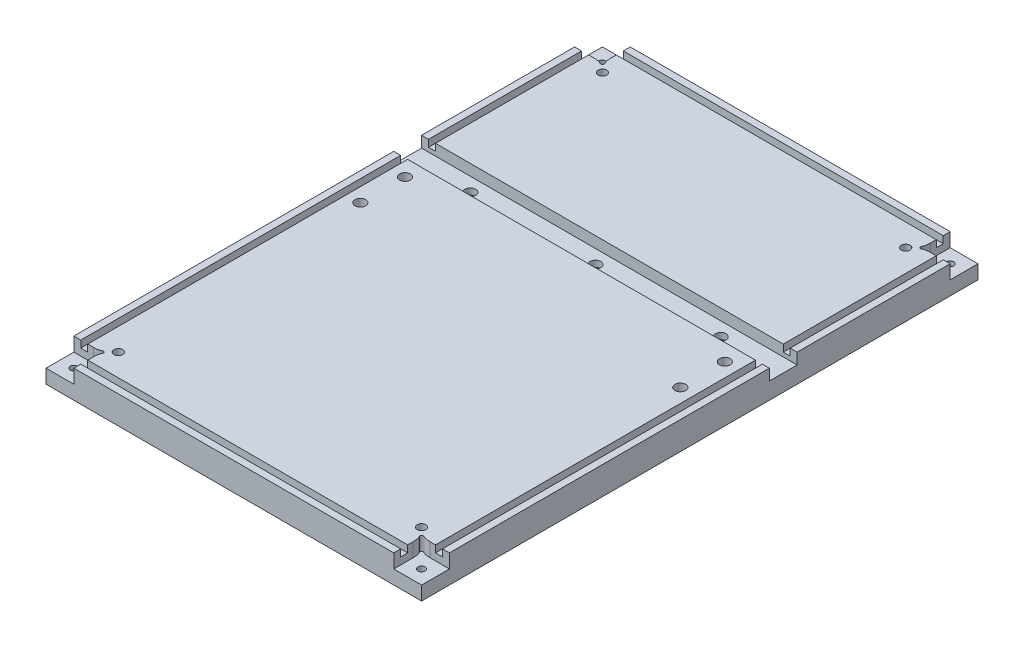
SolidWorks part; units mm, degrees
ref_plane "Front Plane" through (0, 0, 0) normal (0, 0, 1) x (1, 0, 0)
ref_plane "Top Plane" through (0, 0, 0) normal (0, 1, 0) x (1, 0, 0)
ref_plane "Right Plane" through (0, 0, 0) normal (1, 0, 0) x (0, 0, -1)
sketch "Base" plane through (0, 0, 0) normal (0, 1, 0) x (1, 0, 0)
  line L1 (-201.9764, 133.7508) -> (140.9236, 133.7508)
  line L2 (-201.9764, 133.7508) -> (-201.9764, -374.2492)
  line L3 (-201.9764, -374.2492) -> (140.9236, -374.2492)
  line L4 (140.9236, 133.7508) -> (140.9236, -374.2492)
  dimension "D1" = 342.9
  dimension "D2" = 508
extrude "Boss-Extrude1" add sketch "Base" along normal blind 25.4
sketch "Sketch2" plane through (0, 25.4, 0) normal (0, 1, 0) x (1, 0, 0)
  line L1 (172.6736, -31.3492) -> (-233.7264, -31.3492)
  line L2 (172.6736, -31.3492) -> (172.6736, -56.7492)
  line L3 (172.6736, -56.7492) -> (-233.7264, -56.7492)
  line L4 (-233.7264, -31.3492) -> (-233.7264, -56.7492)
  line L6 (140.9236, 133.7508) -> (-201.9764, 133.7508) construction
  line L9 (-30.5264, 133.7508) -> (-30.5264, -374.2492) construction
  line L10 (-201.9764, -374.2492) -> (140.9236, -374.2492) construction
  point P6 (-30.5264, -31.3492)
  dimension "D1" = 317.5
  dimension "D2" = 25.4
  dimension "D3" = 406.4
extrude "Cut-Extrude1" cut sketch "Sketch2" against normal blind 10.16
hole_wizard "CBORE for 3/8 Socket Head Cap Screw4" positions "3DSketch1" profile "Sketch3" counterbore size "3/8" standard "ANSI Inch" end condition up to next
sketch3d "3DSketch1"
  line L3 (-201.9764, 0, -133.7508) -> (-201.9764, 0, 374.2492) construction
  point P0 (83.7736, 0, 44.0492)
  point P2 (-30.5264, 0, 44.0492)
  point P4 (-144.8264, 0, 44.0492)
  dimension "D1" = 12.7
  dimension "D2" = 12.7
  dimension "D3" = 12.7
  dimension "D4" = 171.45
  dimension "D5" = 114.3
  dimension "D6" = 114.3
sketch "Sketch3" plane through (83.7736, 0, 44.0492) normal (1, 0, 0) x (0, 0, -1)
  line L0 (0, 0) -> (0, 15.24)
  line L1 (0, 15.24) -> (4.9022, 15.24)
  line L3 (4.9022, 15.24) -> (4.9022, 9.525)
  line L4 (4.9022, 9.525) -> (7.9375, 9.525)
  line L5 (7.9375, 9.525) -> (7.9375, 0)
  line L7 (7.9375, 0) -> (0, 0)
  line L11 (0, -6.35) -> (0, 107.95) construction
  dimension "Thru Hole Dia." = 9.8044
  dimension "Thru Hole Depth" = 15.24
  dimension "C'Bore Dia." = 15.875
  dimension "C'Bore Depth" = 9.525
hole_wizard "CBORE for 3/8 Socket Head Cap Screw3" positions "Sketch4" profile "Sketch6" counterbore size "3/8" standard "ANSI Inch" end condition up to next
sketch "Sketch4" plane through (0, 0, 0) normal (0, -1, 0) x (-1, 0, 0)
  line L0 (201.9764, -56.7492) -> (-140.9236, -56.7492) construction
  line L1 (-140.9236, -374.2492) -> (-140.9236, 133.7508) construction
  line L3 (201.9764, 133.7508) -> (201.9764, -374.2492) construction
  point P0 (-115.5236, -71.9892)
  point P2 (-115.5236, -112.6292)
  point P4 (176.5764, -71.9892)
  point P6 (176.5764, -112.6292)
  dimension "D1" = 15.24
  dimension "D2" = 25.4
  dimension "D3" = 25.4
  dimension "D4" = 40.64
  dimension "D5" = 15.24
  dimension "D6" = 25.4
  dimension "D7" = 40.64
  dimension "D8" = 25.4
sketch "Sketch6" plane through (115.5236, 0, 71.9892) normal (1, 0, 0) x (0, 0, -1)
  line L0 (0, 0) -> (0, 25.4)
  line L1 (0, 25.4) -> (4.9022, 25.4)
  line L3 (4.9022, 25.4) -> (4.9022, 15.24)
  line L4 (4.9022, 15.24) -> (7.9375, 15.24)
  line L5 (7.9375, 15.24) -> (7.9375, 0)
  line L7 (7.9375, 0) -> (0, 0)
  line L11 (0, -6.35) -> (0, 107.95) construction
  dimension "Thru Hole Dia." = 9.8044
  dimension "Thru Hole Depth" = 25.4
  dimension "C'Bore Dia." = 15.875
  dimension "C'Bore Depth" = 15.24
hole_wizard "CBORE for 1/4 Socket Head Cap Screw1" positions "3DSketch2" profile "Sketch9" counterbore size "1/4" standard "ANSI Inch" end condition up to next
sketch3d "3DSketch2"
  line L0 (140.9236, 0, -133.7508) -> (-201.9764, 0, -133.7508) construction
  line L1 (140.9236, 0, 374.2492) -> (140.9236, 0, -133.7508) construction
  line L2 (-201.9764, 0, -133.7508) -> (-201.9764, 0, 374.2492) construction
  line L3 (-201.9764, 0, 374.2492) -> (140.9236, 0, 374.2492) construction
  point P0 (128.2236, 0, 361.5492)
  point P2 (-189.2764, 0, 361.5492)
  point P4 (-189.2764, 0, -121.0508)
  point P6 (128.2236, 0, -121.0508)
  dimension "D1" = 12.7
  dimension "D2" = 12.7
  dimension "D3" = 12.7
  dimension "D4" = 12.7
  dimension "D5" = 12.7
  dimension "D6" = 12.7
  dimension "D7" = 12.7
  dimension "D8" = 12.7
sketch "Sketch9" plane through (128.2236, 0, 361.5492) normal (1, 0, 0) x (0, 0, -1)
  line L0 (0, 0) -> (0, 25.4)
  line L1 (0, 25.4) -> (3.2639, 25.4)
  line L3 (3.2639, 25.4) -> (3.2639, 6.35)
  line L4 (3.2639, 6.35) -> (5.5562, 6.35)
  line L5 (5.5562, 6.35) -> (5.5562, 0)
  line L7 (5.5562, 0) -> (0, 0)
  line L11 (0, -6.35) -> (0, 107.95) construction
  dimension "Thru Hole Dia." = 6.5278
  dimension "Thru Hole Depth" = 25.4
  dimension "C'Bore Dia." = 11.1125
  dimension "C'Bore Depth" = 6.35
sketch "Sketch8" plane through (0, 25.4, 0) normal (0, 1, 0) x (1, 0, 0)
  line L0 (116.3173, -347.4744) -> (115.5236, -348.8492) construction
  line L1 (140.9236, -374.2492) -> (115.5236, -374.2492)
  line L2 (140.9236, -374.2492) -> (140.9236, -348.8492)
  line L3 (140.9236, -348.8492) -> (123.1436, -348.8492)
  line L4 (115.5236, -374.2492) -> (115.5236, -356.4692)
  line L5 (-201.9764, -374.2492) -> (-176.5764, -374.2492)
  line L6 (-201.9764, -374.2492) -> (-201.9764, -348.8492)
  line L7 (-201.9764, -348.8492) -> (-184.1964, -348.8492)
  line L8 (-176.5764, -374.2492) -> (-176.5764, -356.4692)
  line L9 (-201.9764, 133.7508) -> (-176.5764, 133.7508)
  line L10 (-201.9764, 133.7508) -> (-201.9764, 108.3508)
  line L11 (-201.9764, 108.3508) -> (-184.1964, 108.3508)
  line L12 (-176.5764, 133.7508) -> (-176.5764, 115.9708)
  line L13 (140.9236, 133.7508) -> (115.5236, 133.7508)
  line L14 (140.9236, 133.7508) -> (140.9236, 108.3508)
  line L15 (140.9236, 108.3508) -> (123.1436, 108.3508)
  line L16 (115.5236, 133.7508) -> (115.5236, 115.9708)
  line L17 (115.5236, -348.8492) -> (123.1436, -348.8492) construction
  line L18 (115.5236, -356.4692) -> (115.5236, -348.8492) construction
  line L19 (115.5236, -348.8492) -> (114.1488, -349.6429) construction
  line L20 (115.5236, 108.3508) -> (116.3173, 106.976) construction
  line L21 (115.5236, 108.3508) -> (114.1488, 109.1446) construction
  line L22 (-176.5764, 108.3508) -> (-175.2016, 109.1446) construction
  line L23 (-176.5764, 108.3508) -> (-177.3702, 106.976) construction
  line L24 (-176.5764, -348.8492) -> (-175.2016, -349.6429) construction
  line L25 (-176.5764, -348.8492) -> (-177.3702, -347.4744) construction
  arc A0 (116.3173, -347.4744) -> (114.1488, -349.6429) centre (115.5236, -348.8492) ccw
  arc A1 (114.1488, 109.1446) -> (116.3173, 106.976) centre (115.5236, 108.3508) ccw
  arc A2 (-177.3702, 106.976) -> (-175.2016, 109.1446) centre (-176.5764, 108.3508) ccw
  arc A3 (-175.2016, -349.6429) -> (-177.3702, -347.4744) centre (-176.5764, -348.8492) ccw
  spline S0 degree 3 poles (123.1436, -348.8492) (120.8225, -348.8492) (118.3275, -348.6349) (116.3173, -347.4744) knots 0 0 0 0 1 1 1 1
  spline S1 degree 3 poles (115.5236, -356.4692) (115.5236, -353.9168) (115.3093, -351.6531) (114.1488, -349.6429) knots 0 0 0 0 1 1 1 1
  spline S2 degree 3 poles (123.1436, 108.3508) (120.8225, 108.3508) (118.3275, 108.1366) (116.3173, 106.976) knots 0 0 0 0 1 1 1 1
  spline S3 degree 3 poles (114.1488, 109.1446) (115.3093, 111.1547) (115.5236, 113.6497) (115.5236, 115.9708) knots 0 0 0 0 1 1 1 1
  spline S4 degree 3 poles (-176.5764, 115.9708) (-176.5764, 113.4184) (-176.3621, 111.1547) (-175.2016, 109.1446) knots 0 0 0 0 1 1 1 1
  spline S5 degree 3 poles (-177.3702, 106.976) (-179.3803, 108.1366) (-181.8753, 108.3508) (-184.1964, 108.3508) knots 0 0 0 0 1 1 1 1
  spline S6 degree 3 poles (-175.2016, -349.6429) (-176.7942, -352.4013) (-176.5764, -354.9687) (-176.5764, -356.4692) knots 0 0 0 0 1 1 1 1
  spline S7 degree 3 poles (-177.3702, -347.4744) (-180.1285, -349.0669) (-182.696, -348.8492) (-184.1964, -348.8492) knots 0 0 0 0 1 1 1 1
  point P23 (117.1111, -348.8492)
  point P27 (115.5236, -350.4367)
  dimension "D9" = 7.62
  dimension "D10" = 1.5875
  dimension "D15" = 60
  dimension "D16" = 1.5875
  dimension "D20" = 3.175
  dimension "D25" = 60
  dimension "D28" = 3.175
  dimension "D2" = 25.4
  dimension "D3" = 25.4
  dimension "D4" = 25.4
  dimension "D5" = 25.4
  dimension "D6" = 25.4
  dimension "D7" = 25.4
  dimension "D8" = 25.4
  dimension "D11" = 7.62
  dimension "D12" = 25.4
  dimension "D13" = 60
  dimension "D14" = 60
  dimension "D17" = 60
  dimension "D18" = 7.62
  dimension "D19" = 7.62
  dimension "D21" = 60
  dimension "D22" = 60
  dimension "D23" = 7.62
  dimension "D24" = 7.62
  dimension "D26" = 60
  dimension "D27" = 7.62
  dimension "D29" = 7.62
extrude "Cut-Extrude3" cut sketch "Sketch8" against normal blind 12.7
sketch "Sketch10" plane through (0, 25.4, 0) normal (0, 1, 0) x (1, 0, 0)
  line L1 (128.2236, 108.3508) -> (134.5736, 108.3508)
  line L2 (128.2236, 108.3508) -> (128.2236, -348.8492)
  line L3 (128.2236, -348.8492) -> (134.5736, -348.8492)
  line L4 (134.5736, 108.3508) -> (134.5736, -348.8492)
  line L5 (140.9236, -348.8492) -> (140.9236, -56.7492) construction
  line L8 (-201.9764, 108.3508) -> (-201.9764, -31.3492) construction
  line L9 (-195.6264, 108.3508) -> (-189.2764, 108.3508)
  line L10 (-195.6264, 108.3508) -> (-195.6264, -348.8492)
  line L11 (-195.6264, -348.8492) -> (-189.2764, -348.8492)
  line L12 (-189.2764, 108.3508) -> (-189.2764, -348.8492)
  line L13 (-184.1964, -348.8492) -> (-201.9764, -348.8492) construction
  line L14 (-201.9764, 108.3508) -> (-184.1964, 108.3508) construction
  line L15 (123.1436, 108.3508) -> (140.9236, 108.3508) construction
  line L16 (140.9236, -348.8492) -> (123.1436, -348.8492) construction
  line L17 (-176.5764, 115.9708) -> (-176.5764, 133.7508) construction
  line L18 (-176.5764, 127.4008) -> (115.5236, 127.4008)
  line L19 (-176.5764, 127.4008) -> (-176.5764, 121.0508)
  line L20 (-176.5764, 121.0508) -> (115.5236, 121.0508)
  line L21 (115.5236, 127.4008) -> (115.5236, 121.0508)
  line L22 (115.5236, 133.7508) -> (115.5236, 115.9708) construction
  line L23 (115.5236, 133.7508) -> (-176.5764, 133.7508) construction
  line L24 (-176.5764, -374.2492) -> (-176.5764, -356.4692) construction
  line L25 (-176.5764, -361.5492) -> (115.5236, -361.5492)
  line L26 (-176.5764, -361.5492) -> (-176.5764, -367.8992)
  line L27 (-176.5764, -367.8992) -> (115.5236, -367.8992)
  line L28 (115.5236, -361.5492) -> (115.5236, -367.8992)
  line L29 (115.5236, -356.4692) -> (115.5236, -374.2492) construction
  line L30 (-176.5764, -374.2492) -> (115.5236, -374.2492) construction
  dimension "D1" = 6.35
  dimension "D2" = 6.35
  dimension "D3" = 6.35
  dimension "D4" = 6.35
  dimension "D5" = 6.35
  dimension "D6" = 6.35
  dimension "D7" = 6.35
  dimension "D8" = 6.35
extrude "Cut-Extrude4" cut sketch "Sketch10" against normal blind 6.35
hole_wizard "3/8-16 Tapped Hole2" positions "Sketch17" profile "Sketch18" tap size "3/8-16" standard "ANSI Inch" end condition up to next
sketch "Sketch17" plane through (0, 0, 0) normal (0, -1, 0) x (-1, 0, 0)
  line L0 (-140.9236, 133.7508) -> (201.9764, 133.7508) construction
  line L1 (-140.9236, -374.2492) -> (-140.9236, 133.7508) construction
  line L2 (201.9764, 133.7508) -> (201.9764, -374.2492) construction
  line L3 (201.9764, -374.2492) -> (-140.9236, -374.2492) construction
  point P0 (-107.9036, -341.2292)
  point P2 (168.9564, -341.2292)
  point P4 (168.9564, 100.7308)
  point P6 (-107.9036, 100.7308)
  dimension "D1" = 33.02
  dimension "D2" = 33.02
  dimension "D3" = 33.02
  dimension "D4" = 33.02
  dimension "D5" = 33.02
  dimension "D6" = 33.02
  dimension "D7" = 33.02
  dimension "D8" = 33.02
sketch "Sketch18" plane through (107.9036, 0, 341.2292) normal (1, 0, 0) x (0, 0, -1)
  line L0 (0, 0) -> (0, 25.4)
  line L1 (0, 25.4) -> (3.9687, 25.4)
  line L2 (3.9687, 25.4) -> (3.9687, 0)
  line L5 (3.9687, 0) -> (0, 0)
  line L11 (0, -6.35) -> (0, 107.95) construction
  dimension "Thru Tap Drill Dia." = 7.9375
  dimension "Thru Tap Drill Depth" = 25.4
cosmetic thread "Hole Thread5" parameters "D2"=9.525
cosmetic thread "Hole Thread6" parameters "D2"=9.525
cosmetic thread "Hole Thread7" parameters "D2"=9.525
cosmetic thread "Hole Thread8" parameters "D2"=9.525
sketch "Sketch19" plane through (0, 0, 0) normal (0, -1, 0) x (1, 0, 0)
  circle A0 centre (-168.9564, -100.7308) radius 9.525
  circle A1 centre (-168.9564, 341.2292) radius 9.525
  circle A2 centre (107.9036, 341.2292) radius 9.525
  circle A3 centre (108.2173, -100.7308) radius 9.525
  dimension "D1" = 19.05
  dimension "D2" = 19.05
  dimension "D3" = 19.05
  dimension "D4" = 19.05
extrude "Cut-Extrude5" cut sketch "Sketch19" against normal blind 1.27
